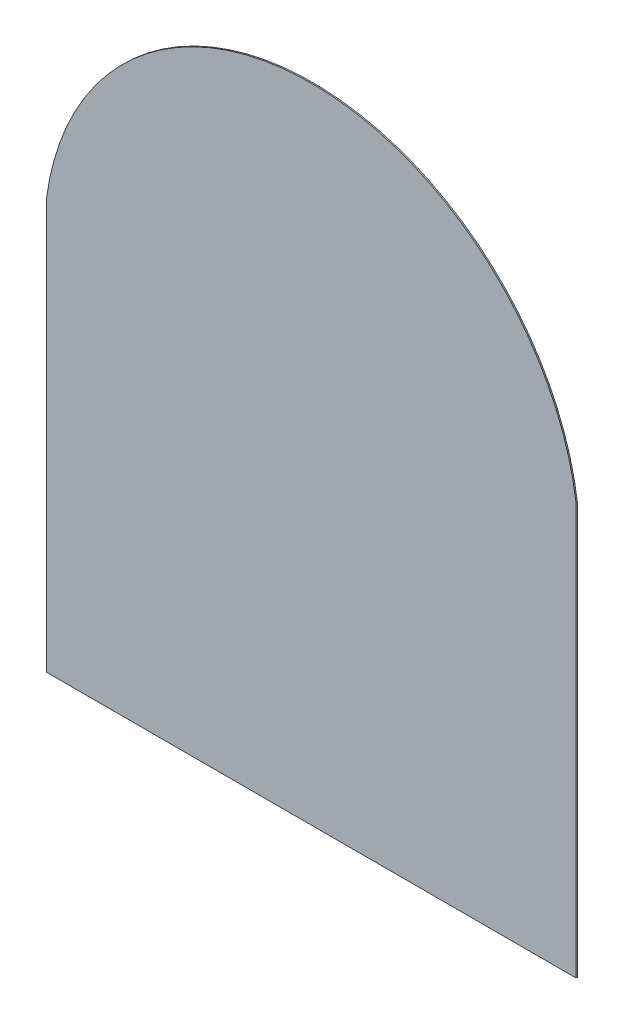
SolidWorks part; units mm, degrees
ref_plane "Front Plane" through (0, 0, 0) normal (0, 0, 1) x (1, 0, 0)
ref_plane "Top Plane" through (0, 0, 0) normal (0, 1, 0) x (1, 0, 0)
ref_plane "Right Plane" through (0, 0, 0) normal (1, 0, 0) x (0, 0, -1)
sketch "Sketch1" plane through (0, 0, 0) normal (0, 0, 1) x (1, 0, 0)
  line L2 (1030, 800) -> (1030, -800)
  line L3 (1030, -800) -> (-1030, -800)
  line L4 (-1030, 800) -> (-1030, -800)
  line L5 (1030, 800) -> (-1030, -800) construction
  line L6 (1030, -800) -> (-1030, 800) construction
  arc A1 (-1030, 800) -> (1030, 800) centre (0, 660.6111) cw
  point P0 (0, 0)
  point P1 (0, 0)
  point P10 (0, 1700)
  dimension "D1" = 2060
  dimension "D2" = 900
  dimension "D3" = 1600
extrude "Boss-Extrude1" add sketch "Sketch1" along normal mid plane 5
